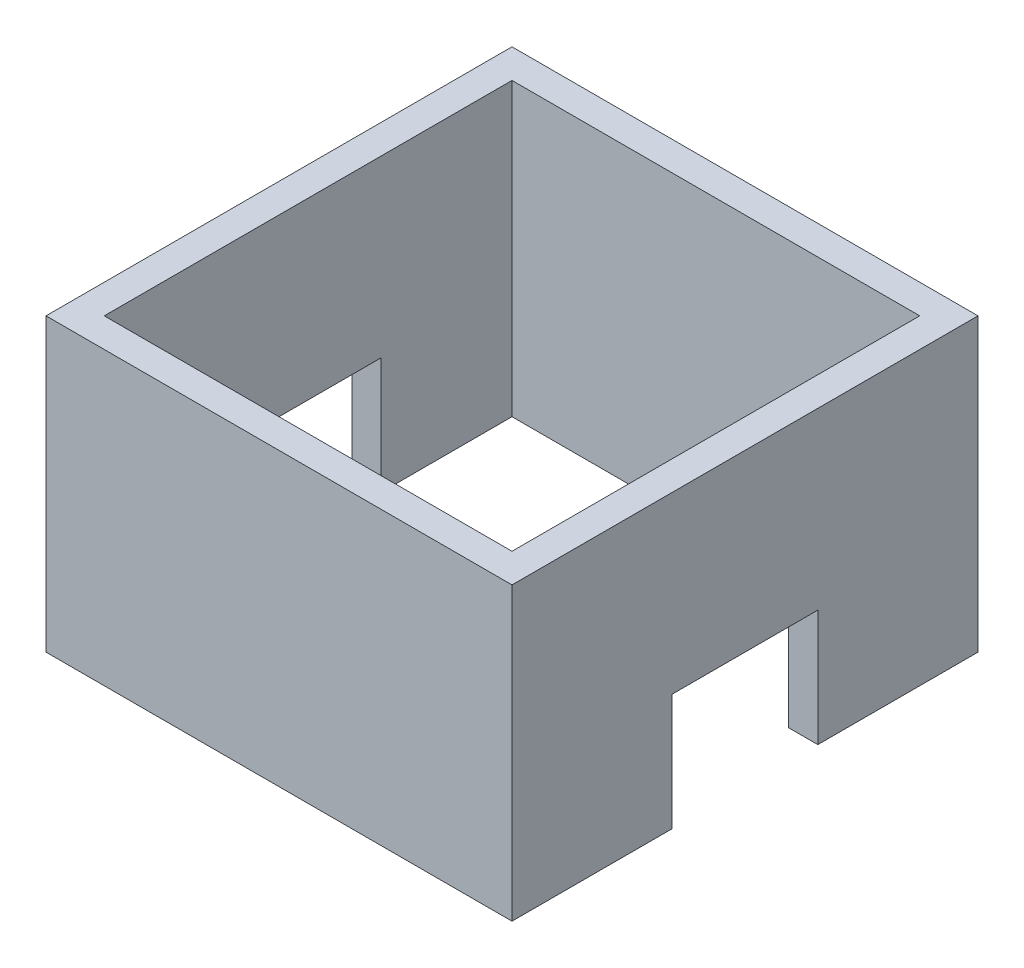
SolidWorks part; units mm, degrees
ref_plane "Front Plane" through (0, 0, 0) normal (0, 0, 1) x (1, 0, 0)
ref_plane "Top Plane" through (0, 0, 0) normal (0, 1, 0) x (1, 0, 0)
ref_plane "Right Plane" through (0, 0, 0) normal (1, 0, 0) x (0, 0, -1)
sketch "Sketch1" plane through (0, 0, 0) normal (0, 1, 0) x (1, 0, 0)
  line L0 (-16, -16) -> (-16, 16)
  line L1 (14, -14) -> (-14, -14)
  line L2 (14, -14) -> (14, 14)
  line L3 (14, 14) -> (-14, 14)
  line L4 (-14, -14) -> (-14, 14)
  line L5 (14, -14) -> (-14, 14) construction
  line L6 (14, 14) -> (-14, -14) construction
  line L7 (16, 16) -> (-16, 16)
  line L8 (16, -16) -> (16, 16)
  line L9 (16, -16) -> (-16, -16)
  point P0 (0, 0)
  dimension "D1" = 28
  dimension "D2" = 2
extrude "Boss-Extrude1" add sketch "Sketch1" along normal blind 20
sketch "Sketch2" plane through (16, 0, 0) normal (1, 0, 0) x (0, 0, -1)
  line L0 (-16, 0) -> (16, 0) construction
  line L1 (5, 8) -> (-5, 8)
  line L2 (5, 8) -> (5, 0)
  line L3 (5, 0) -> (-5, 0)
  line L4 (-5, 8) -> (-5, 0)
  line L5 (5, 8) -> (-5, 0) construction
  line L6 (5, 0) -> (-5, 8) construction
  line L7 (0, 4) -> (0, 0) construction
  point P0 (0, 4)
  dimension "D1" = 8
  dimension "D2" = 10
extrude "Cut-Extrude1" cut sketch "Sketch2" against normal through all
